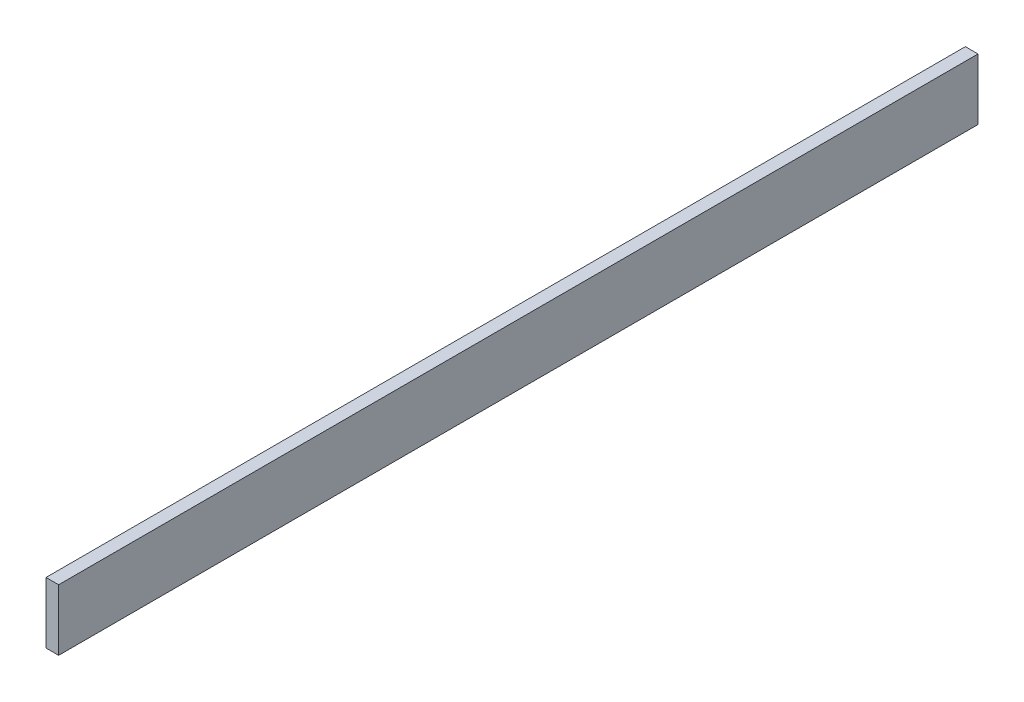
SolidWorks part; units mm, degrees
ref_plane "Front Plane" through (0, 0, 0) normal (0, 0, 1) x (1, 0, 0)
ref_plane "Top Plane" through (0, 0, 0) normal (0, 1, 0) x (1, 0, 0)
ref_plane "Right Plane" through (0, 0, 0) normal (1, 0, 0) x (0, 0, -1)
sketch "Sketch1" plane through (0, 0, 0) normal (1, 0, 0) x (0, 0, -1)
  line L1 (-474.1718, 50.8) -> (2294.4282, 50.8)
  line L2 (-474.1718, 50.8) -> (-474.1718, 234.95)
  line L3 (-474.1718, 234.95) -> (2294.4282, 234.95)
  line L4 (2294.4282, 50.8) -> (2294.4282, 234.95)
  dimension "D1" = 184.15
  dimension "D2" = 2768.6
extrude "Boss-Extrude1" add sketch "Sketch1" along normal blind 38.1
